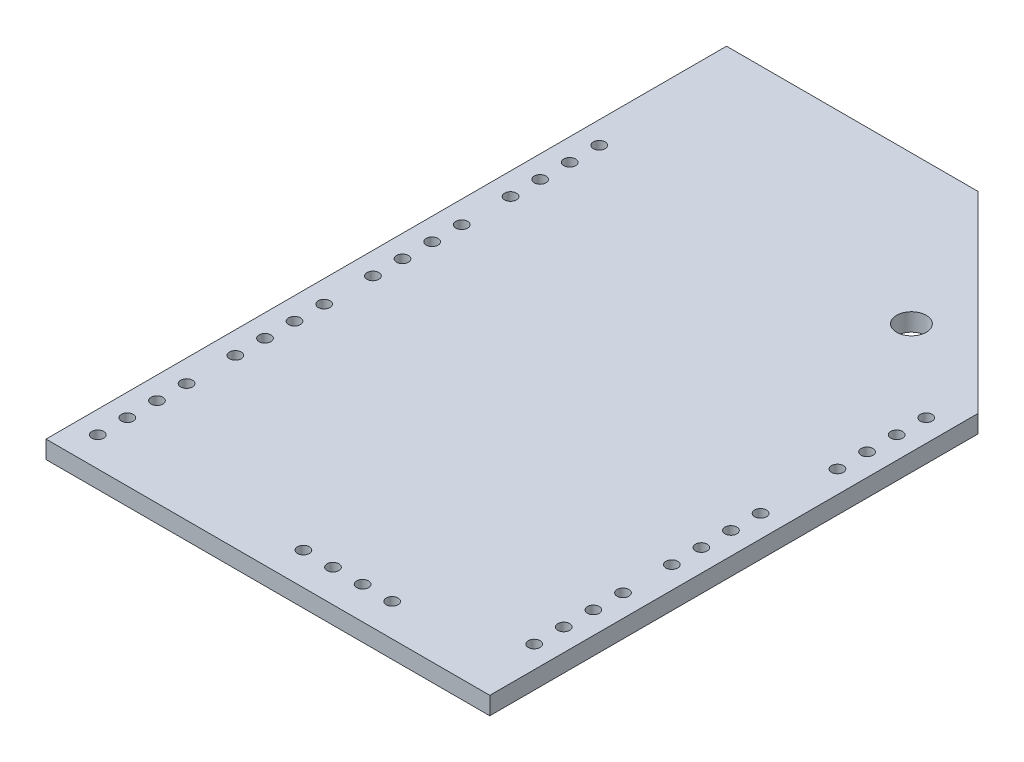
SolidWorks part; units mm, degrees
ref_plane "Front Plane" through (0, 0, 0) normal (0, 0, 1) x (1, 0, 0)
ref_plane "Top Plane" through (0, 0, 0) normal (0, 1, 0) x (1, 0, 0)
ref_plane "Right Plane" through (0, 0, 0) normal (1, 0, 0) x (0, 0, -1)
sketch "Sketch1" plane through (0, 0, 0) normal (0, 1, 0) x (1, 0, 0)
  line L0 (0, 0) -> (0, 46)
  line L1 (0, 46) -> (17, 46)
  line L2 (17, 46) -> (30, 33)
  line L3 (30, 33) -> (30, 0)
  line L4 (30, 0) -> (0, 0)
  dimension "D1" = 30
  dimension "D2" = 46
  dimension "D3" = 17
  dimension "D4" = 33
extrude "Boss-Extrude1" add sketch "Sketch1" along normal blind 1.2
sketch "Sketch2" plane through (0, 1.2, 0) normal (0, 1, 0) x (1, 0, 0)
  line L0 (0, 46) -> (0, 0) construction
  line L1 (0, 0) -> (30, 0) construction
  circle A0 centre (22.5, 36) radius 1
  dimension "D3" = 2
  dimension "D1" = 22.5
  dimension "D2" = 36
extrude "Cut-Extrude1" cut sketch "Sketch2" against normal up to next
sketch "Sketch3" plane through (0, 1.2, 0) normal (0, 1, 0) x (1, 0, 0)
  line L0 (0, 0) -> (30, 0) construction
  line L1 (0, 46) -> (0, 0) construction
  circle A0 centre (1.5, 2) radius 0.4
  circle A1 centre (1.5, 4) radius 0.4
  circle A2 centre (1.5, 6) radius 0.4
  circle A3 centre (1.5, 8) radius 0.4
  dimension "D1" = 0.8
  dimension "D2" = 2
  dimension "D3" = 1.5
  dimension "D5" = 2
  dimension "D4" = 4
extrude "Cut-Extrude2" cut sketch "Sketch3" against normal up to next (1.2 mm away)
pattern_linear "LPattern1" count 4 spacing 9.3 along (0, 0, -1) of "Cut-Extrude2"
sketch "Sketch4" plane through (0, 1.2, 0) normal (0, 1, 0) x (1, 0, 0)
  line L0 (0, 0) -> (30, 0) construction
  line L1 (30, 0) -> (30, 33) construction
  circle A0 centre (28.5, 4.5) radius 0.4
  circle A1 centre (1.5, 2) radius 0.4 construction
  circle A2 centre (28.5, 6.5) radius 0.4
  circle A3 centre (28.5, 8.5) radius 0.4
  circle A4 centre (28.5, 10.5) radius 0.4
  dimension "D1" = 4.5
  dimension "D2" = 1.5
  dimension "D4" = 2
  dimension "D3" = 4
extrude "Cut-Extrude3" cut sketch "Sketch4" against normal up to next (1.2 mm away)
pattern_linear "LPattern2" count 2 spacing 9.3 along (0, 0, -1) of "Cut-Extrude3"
pattern_linear "LPattern3" count 2 spacing 20.5 along (0, 0, -1) of "Cut-Extrude3"
sketch "Sketch5" plane through (0, 1.2, 0) normal (0, 1, 0) x (1, 0, 0)
  line L0 (0, 0) -> (30, 0) construction
  line L1 (0, 46) -> (0, 0) construction
  circle A0 centre (15.2, 2.2) radius 0.4
  circle A1 centre (1.5, 2) radius 0.4 construction
  circle A2 centre (17.2, 2.2) radius 0.4
  circle A3 centre (19.2, 2.2) radius 0.4
  circle A4 centre (21.2, 2.2) radius 0.4
  dimension "D1" = 2.2
  dimension "D2" = 15.2
  dimension "D4" = 2
  dimension "D3" = 4
extrude "Cut-Extrude4" cut sketch "Sketch5" against normal up to next
